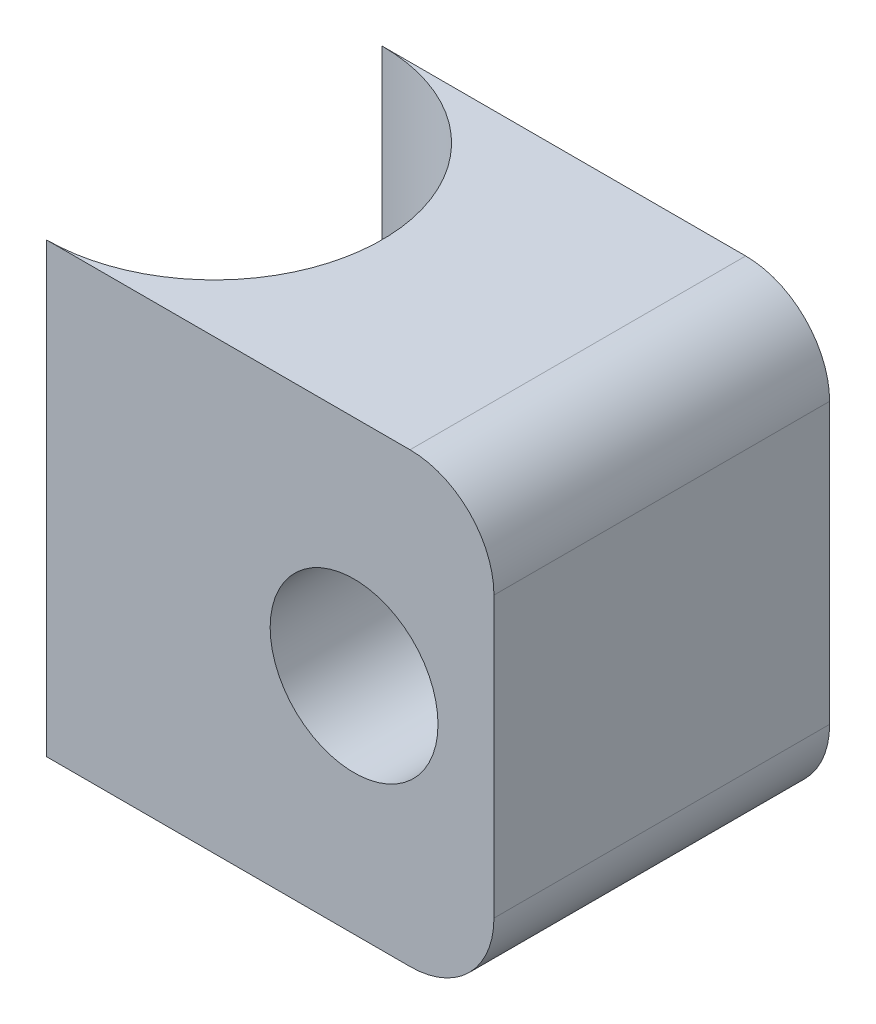
SolidWorks part; units mm, degrees
material "Plain Carbon Steel"
ref_plane "Front Plane" through (0, 0, 0) normal (0, 0, 1) x (1, 0, 0)
ref_plane "Top Plane" through (0, 0, 0) normal (0, 1, 0) x (1, 0, 0)
ref_plane "Right Plane" through (0, 0, 0) normal (1, 0, 0) x (0, 0, -1)
sketch "Sketch1" plane through (0, 0, 0) normal (0, 0, 1) x (1, 0, 0)
  line L0 (0, 0) -> (0, 8)
  line L1 (0, 0) -> (8, 0)
  line L2 (8, 0) -> (8, 8)
  line L3 (8, 8) -> (0, 8)
  dimension "D1" = 8
  dimension "D2" = 8
extrude "Boss-Extrude1" add sketch "Sketch1" along normal blind 6
sketch "Sketch2" plane through (0, 0, 0) normal (0, 0, -1) x (-1, 0, 0)
  line L0 (-8, 4) -> (-5.5, 4)
  line L1 (-8, 0) -> (-8, 8) construction
  circle A0 centre (-5.5, 4) radius 1.5
  dimension "D2" = 3
  dimension "D1" = 2.5
extrude "Cut-Extrude1" cut sketch "Sketch2" against normal blind 6
sketch "Sketch3" plane through (0, 0, 0) normal (0, -1, 0) x (1, 0, 0)
  line L0 (0, 6) -> (0, 0)
  arc A0 (0, 6) -> (0, 0) centre (0, 3) cw
extrude "Cut-Extrude3" cut sketch "Sketch3" against normal blind 9
sketch "Sketch4" plane through (0, 0, 0) normal (0, 0, -1) x (-1, 0, 0)
  circle A0 centre (-5.5, 4) radius 1.5
extrude "Boss-Extrude3" add sketch "Sketch4" against normal blind 1
fillet "Fillet1" radius 1.5 2 edges at (8, 8, 3) (8, 0, 3)
